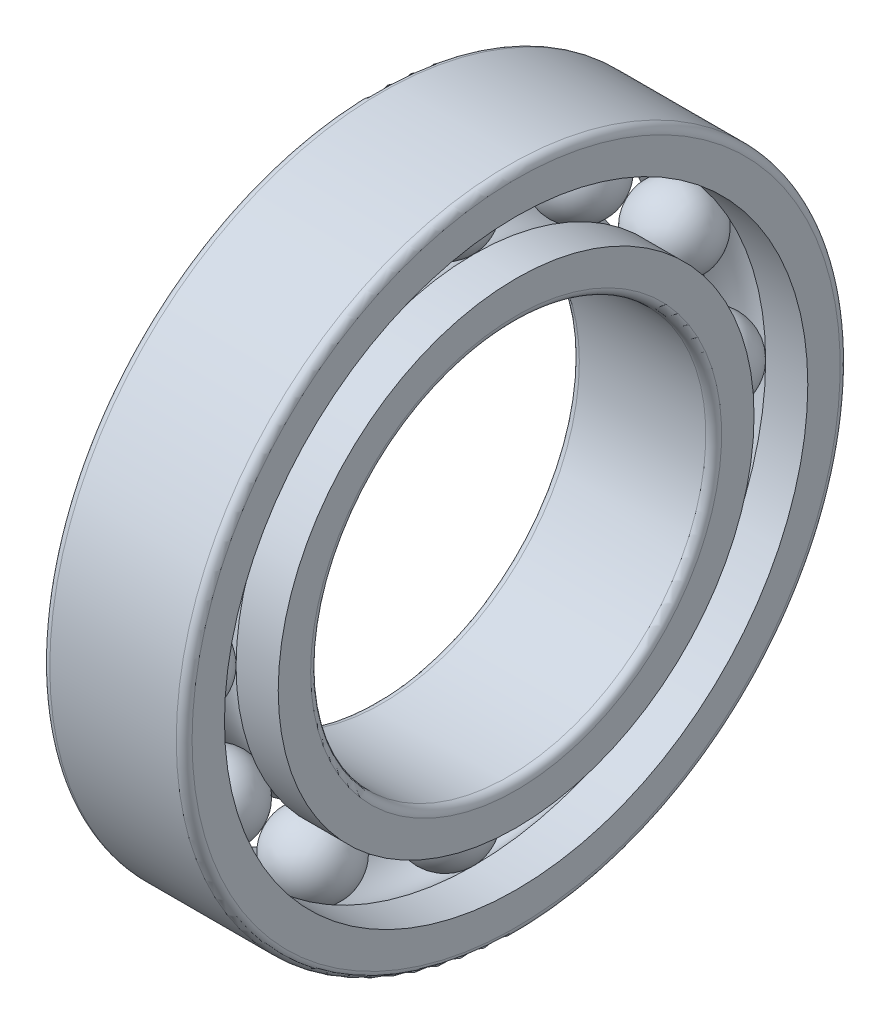
SolidWorks part; units mm, degrees
ref_plane "Спереди" through (0, 0, 0) normal (0, 0, 1) x (1, 0, 0)
ref_plane "Сверху" through (0, 0, 0) normal (0, 1, 0) x (1, 0, 0)
ref_plane "Справа" through (0, 0, 0) normal (1, 0, 0) x (0, 0, -1)
sketch "Эскиз1" plane through (0, 0, 0) normal (0, 0, 1) x (1, 0, 0)
  line L0 (0, 0) -> (13979.1977, 0) construction
  line L1 (0, 15.05) -> (0, 12.5)
  line L2 (0, 12.5) -> (9, 12.5)
  line L3 (9, 12.5) -> (9, 15.05)
  line L6 (9, 18.45) -> (9, 21)
  line L7 (9, 21) -> (0, 21)
  line L8 (0, 21) -> (0, 18.45)
  line L9 (0, 12.5) -> (9, 21) construction
  line L10 (0, 21) -> (9, 12.5) construction
  line L11 (0, 18.45) -> (2.667, 18.45)
  line L12 (6.333, 18.45) -> (9, 18.45)
  line L13 (0, 15.05) -> (2.667, 15.05)
  line L14 (6.333, 15.05) -> (9, 15.05)
  arc A0 (2.667, 18.45) -> (6.333, 18.45) centre (4.5, 16.75) cw
  arc A1 (2.667, 15.05) -> (6.333, 15.05) centre (4.5, 16.75) ccw
  point P16 (2.1727, 18.45)
  dimension "D5" = 2.5
  dimension "D1" = 42
  dimension "D2" = 9
  dimension "D3" = 25
  dimension "D4" = 2.55
revolve "Повернуть1" add sketch "Эскиз1" angle 360 about L0
fillet "Скругление1" radius 0.5 2 edges at (9, 0, 21) (0, 0, 21)
fillet "Скругление2" radius 0.5 2 edges at (9, 0, 12.5) (0, 0, 12.5)
sketch "Эскиз2" plane through (0, 0, 0) normal (0, 0, 1) x (1, 0, 0)
  line L0 (2.667, 15.05) -> (6.333, 18.45) construction
  line L1 (2.667, 18.45) -> (6.333, 15.05) construction
  line L2 (2, 16.75) -> (7, 16.75) construction
  line L3 (2, 16.75) -> (7, 16.75)
  arc A0 (7, 16.75) -> (2, 16.75) centre (4.5, 16.75) ccw
  point P13 (0, 0)
  point P14 (7, 16.75)
  point P15 (4.5, 16.75)
  point P16 (7, 16.75)
  dimension "D2" = 2.5
  dimension "D1" = 5
revolve "Повернуть4" add sketch "Эскиз2" angle 360 about L2
pattern_circular "Круговой массив1" count 12 over 360 about axis through (0, 0, 0) along (1, 0, 0) of bodies 105
